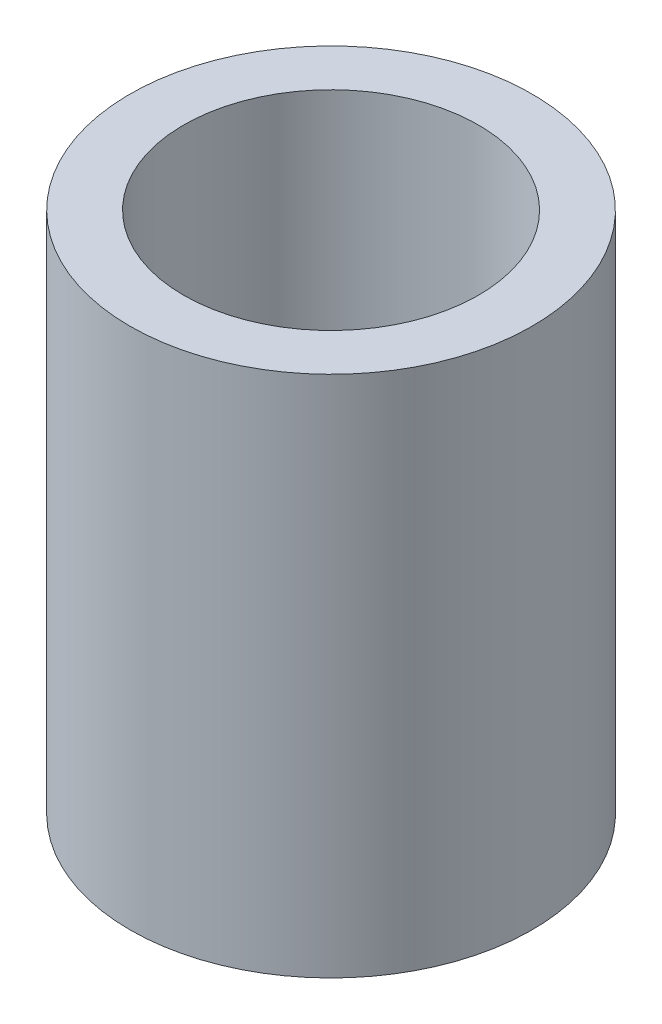
SolidWorks part; units mm, degrees
ref_plane "Alzado" through (0, 0, 0) normal (0, 0, 1) x (1, 0, 0)
ref_plane "Planta" through (0, 0, 0) normal (0, 1, 0) x (1, 0, 0)
ref_plane "Vista lateral" through (0, 0, 0) normal (1, 0, 0) x (0, 0, -1)
sketch "Croquis1" plane through (0, 0, 0) normal (0, 1, 0) x (1, 0, 0)
  circle A0 centre (0, 0) radius 7.5
  circle A1 centre (0, 0) radius 5.5
  dimension "D1" = 11
  dimension "D2" = 2
extrude "Saliente-Extruir1" add sketch "Croquis1" along normal blind 19.5
